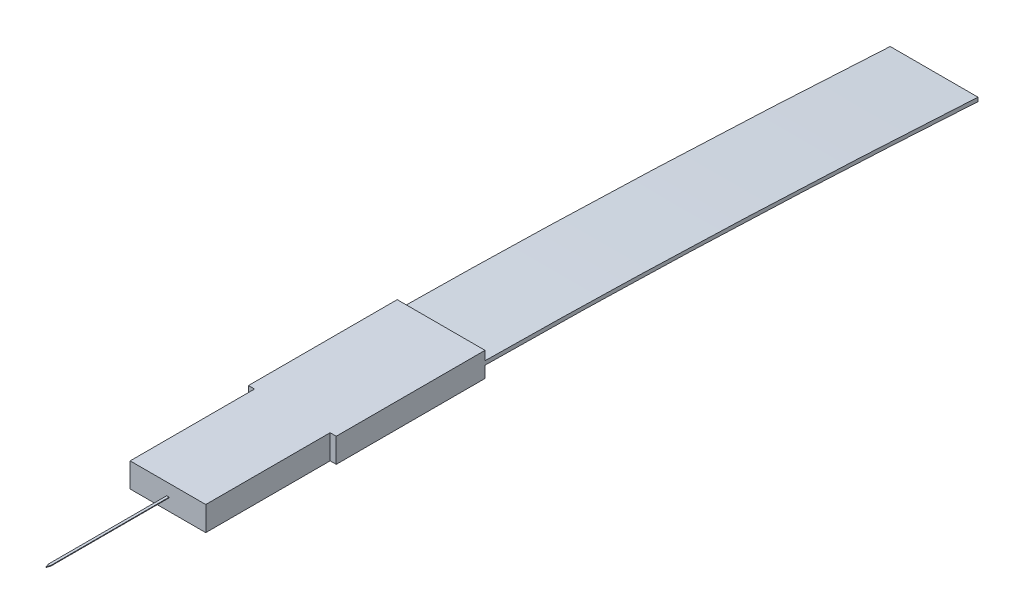
SolidWorks part; units mm, degrees
ref_plane "Front Plane" through (0, 0, 0) normal (0, 0, 1) x (1, 0, 0)
ref_plane "Top Plane" through (0, 0, 0) normal (0, 1, 0) x (1, 0, 0)
ref_plane "Right Plane" through (0, 0, 0) normal (1, 0, 0) x (0, 0, -1)
sketch "Sketch1" plane through (0, 0, 0) normal (0, 1, 0) x (1, 0, 0)
  line L0 (-3.1, -6.1) -> (3.1, -6.1)
  line L1 (-3.6, -6.1) -> (3.6, -6.1)
  line L2 (-3.6, -6.1) -> (-3.6, 6.1)
  line L3 (-3.6, 6.1) -> (3.6, 6.1)
  line L4 (3.6, -6.1) -> (3.6, 6.1)
  line L5 (0, 6.1) -> (0, -6.1) construction
  line L6 (-3.6, 0) -> (3.6, 0) construction
  line L8 (-3.1, -6.1) -> (3.1, -6.1)
  line L9 (-3.1, -6.1) -> (-3.1, -16.3)
  line L10 (-3.1, -16.3) -> (3.1, -16.3)
  line L11 (3.1, -6.1) -> (3.1, -16.3)
  point P0 (0, 0)
  point P7 (0, -6.1)
  dimension "D1" = 7.2
  dimension "D2" = 12.2
  dimension "D3" = 10.2
extrude "Boss-Extrude1" add sketch "Sketch1" along normal blind 2 contours L1 L4 L3 L2 L0 | L11 L0 L9 L10
sketch "Sketch2" plane through (0, 0, -6.1) normal (0, 0, -1) x (-1, 0, 0)
  line L0 (0, 0) -> (0, 2) construction
  line L1 (3.6, 0) -> (-3.6, 0) construction
  line L2 (3.6, 2) -> (-3.6, 2) construction
  line L4 (-3.55, 0.8732) -> (3.55, 0.8732)
  line L5 (-3.55, 0.8732) -> (-3.55, 1.1268)
  line L6 (-3.55, 1.1268) -> (3.55, 1.1268)
  line L7 (3.55, 0.8732) -> (3.55, 1.1268)
  line L8 (0, 1.1268) -> (0, 0.8732) construction
  line L9 (-3.55, 1) -> (3.55, 1) construction
  point P6 (0, 1)
  dimension "D1" = 7.1
extrude "Boss-Extrude2" [suppressed] add sketch "Sketch2" along normal blind 30
sketch "Sketch3" plane through (0, 0, 16.3) normal (0, 0, 1) x (1, 0, 0)
  line L0 (0, 0) -> (0, 2) construction
  line L1 (-3.1, 2) -> (3.1, 2) construction
  line L3 (-0.1, 0.975) -> (0.1, 0.975)
  line L4 (-0.1, 0.975) -> (-0.1, 1.025)
  line L5 (-0.1, 1.025) -> (0.1, 1.025)
  line L6 (0.1, 0.975) -> (0.1, 1.025)
  line L7 (0, 1.025) -> (0, 0.975) construction
  line L8 (-0.1, 1) -> (0.1, 1) construction
  point P5 (0, 1)
  dimension "D1" = 0.05
  dimension "D2" = 0.2
extrude "Boss-Extrude3" add sketch "Sketch3" along normal blind 10
sketch "Sketch4" plane through (0, 0.975, 0) normal (0, -1, 0) x (1, 0, 0)
  line L0 (0, 26.3) -> (0, 26) construction
  line L1 (-0.1, 26.3) -> (0.1, 26.3) construction
  line L2 (-0.1, 26) -> (0.1, 26) construction
  line L3 (-0.1, 26.3) -> (-0.1, 16.3) construction
  line L4 (0.1, 26.3) -> (0.1, 16.3) construction
  line L5 (-0.1, 26) -> (0, 26.3)
  line L6 (0, 26.3) -> (0.1, 26)
  line L7 (-0.1, 26) -> (-0.1, 26.3)
  line L8 (-0.1, 26.3) -> (0.1, 26.3)
  line L9 (0.1, 26.3) -> (0.1, 26)
  line M3 (0.1, 16.3) -> (0.1, 26.3)
  line M4 (0.1, 26.3) -> (-0.1, 26.3)
  line M5 (-0.1, 26.3) -> (-0.1, 16.3)
  dimension "D1" = 0.3
extrude "Cut-Extrude1" cut sketch "Sketch4" against normal up to surface (0.05 mm away) contours L6 M4 M3 | L5 M5 M4 up to face at (0, 1.025, 21.3)
sketch "Sketch5" plane through (3.6, 0, 0) normal (1, 0, 0) x (0, 0, -1)
  line L1 (6.1, 2) -> (6.1, 0) construction
  line L2 (6.1, 1.2618) -> (6.1, 0.9423)
  line L3 (46.5259, -0.2347) -> (46.5259, -0.5541)
  spline S0 degree 2 poles (6.1, 0.9423) (24.5183, 0.8103) (46.5259, -0.5541) knots 0 0 0 1 1 1
  spline S1 degree 2 poles (6.1, 1.2618) (24.5624, 1.0834) (46.5259, -0.2347) knots 0 0 0 1 1 1
extrude "Boss-Extrude4" add sketch "Sketch5" against normal blind 7.2
